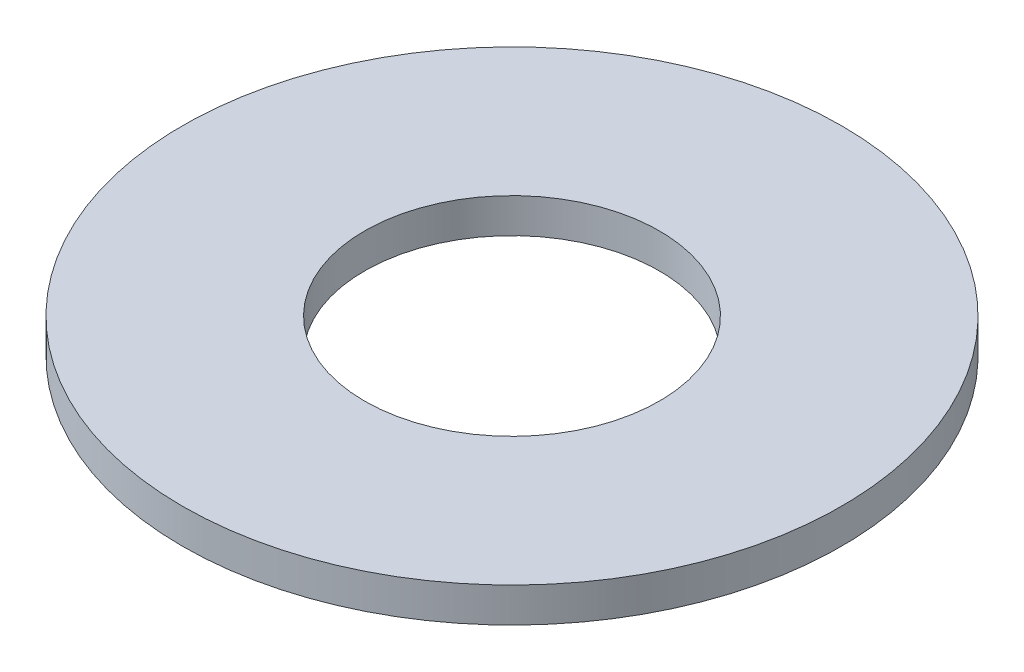
SolidWorks part; units mm, degrees
material "6061 Alloy"
ref_plane "Front Plane" through (0, 0, 0) normal (0, 0, 1) x (1, 0, 0)
ref_plane "Top Plane" through (0, 0, 0) normal (0, 1, 0) x (1, 0, 0)
ref_plane "Right Plane" through (0, 0, 0) normal (1, 0, 0) x (0, 0, -1)
sketch "Sketch1" plane through (0, 0, 0) normal (0, 1, 0) x (1, 0, 0)
  circle A0 centre (0, 0) radius 2.159
  circle A1 centre (0, 0) radius 4.826
  dimension "D1" = 4.318
  dimension "D2" = 9.652
extrude "Boss-Extrude1" add sketch "Sketch1" along normal blind 0.508
